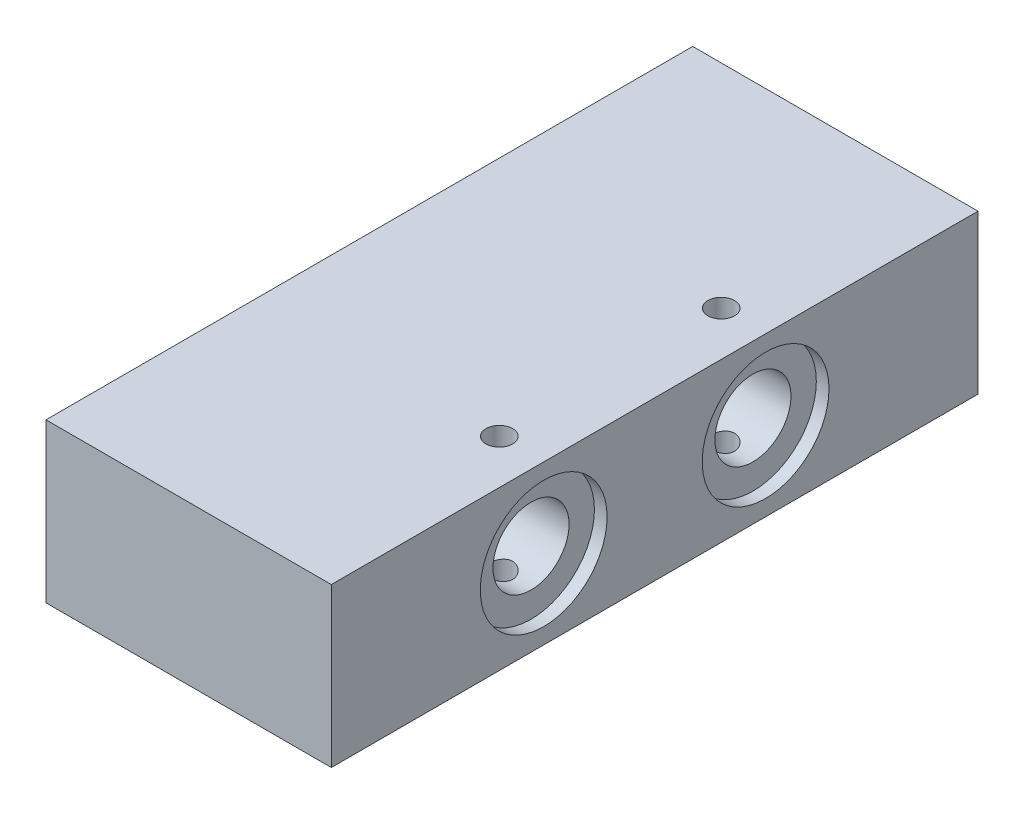
SolidWorks part; units mm, degrees
ref_plane "Front Plane" through (0, 0, 0) normal (0, 0, 1) x (1, 0, 0)
ref_plane "Top Plane" through (0, 0, 0) normal (0, 1, 0) x (1, 0, 0)
ref_plane "Right Plane" through (0, 0, 0) normal (1, 0, 0) x (0, 0, -1)
sketch "Sketch1" plane through (0, 0, 0) normal (0, 1, 0) x (1, 0, 0)
  line L1 (-22.5, -51) -> (22.5, -51)
  line L2 (-22.5, -51) -> (-22.5, 51)
  line L3 (-22.5, 51) -> (22.5, 51)
  line L4 (22.5, -51) -> (22.5, 51)
  line L5 (-22.5, -51) -> (22.5, 51) construction
  line L6 (-22.5, 51) -> (22.5, -51) construction
  point P0 (0, 0)
  dimension "D1" = 45
  dimension "D2" = 102
extrude "Boss-Extrude1" add sketch "Sketch1" along normal blind 25
hole_wizard "M5 Tapped Hole3" positions "Sketch12" profile "Sketch13" tap size "M5" standard "DIN" end condition through all
sketch "Sketch12" plane through (0, 25, 0) normal (0, 1, 0) x (1, 0, 0)
  line L0 (22.5, -51) -> (22.5, 51) construction
  line L1 (-22.5, -51) -> (22.5, -51) construction
  point P0 (15.5, 17.5)
  point P2 (15.5, -17.5)
  dimension "D1" = 7
  dimension "D2" = 7
  dimension "D3" = 33.5
  dimension "D4" = 35
sketch "Sketch13" plane through (15.5, 25, -17.5) normal (1, 0, 0) x (0, 0, 1)
  line L0 (0, 0) -> (0, 25)
  line L1 (0, 25) -> (2.1, 25)
  line L2 (2.1, 25) -> (2.1, 0)
  line L5 (2.1, 0) -> (0, 0)
  line L11 (0, -6.35) -> (0, 107.95) construction
  dimension "Thru Tap Drill Dia." = 4.2
  dimension "Thru Tap Drill Depth" = 25
cosmetic thread "Hole Thread9" parameters "D2"=5
cosmetic thread "Hole Thread10" parameters "D2"=5
sketch "Sketch27" plane through (-22.5, 0, 0) normal (-1, 0, 0) x (0, 0, 1)
  line L0 (51, 25) -> (51, 0) construction
  line L1 (-51, 25) -> (51, 25) construction
  circle A0 centre (-17.5, 12.5) radius 6
  circle A1 centre (17.5, 12.5) radius 6
  dimension "D1" = 12
  dimension "D2" = 12
  dimension "D5" = 12.5
  dimension "D3" = 33.5
  dimension "D4" = 35
  dimension "D6" = 12.5
extrude "Cut-Extrude1" cut sketch "Sketch27" against normal blind 74
sketch "Sketch28" plane through (-22.5, 0, 0) normal (-1, 0, 0) x (0, 0, 1)
  circle A0 centre (-17.5, 12.5) radius 10
  circle A1 centre (17.5, 12.5) radius 10
  dimension "D1" = 20
  dimension "D2" = 20
extrude "Cut-Extrude3" cut sketch "Sketch28" against normal blind 2
sketch "Sketch30" plane through (22.5, 0, 0) normal (1, 0, 0) x (0, 0, -1)
  circle A0 centre (-17.5, 12.5) radius 10
  circle A1 centre (17.5, 12.5) radius 10
  dimension "D1" = 20
  dimension "D2" = 20
extrude "Cut-Extrude4" cut sketch "Sketch30" against normal blind 2
hole_wizard "M5 Tapped Hole4" positions "Sketch31" profile "Sketch32" tap size "M5" standard "DIN"
sketch "Sketch31" plane through (0, 0, -51) normal (0, 0, -1) x (-1, 0, 0)
  line L0 (22.5, 25) -> (22.5, 0) construction
  line L1 (-22.5, 25) -> (-22.5, 0) construction
  line L3 (-22.5, 0) -> (22.5, 0) construction
  line L4 (-22.5, 25) -> (22.5, 25) construction
  point P0 (-18, 5)
  point P2 (18, 20)
  point P13 (-15.7032, 0)
  point P20 (-56.0486, 27.3495)
  dimension "D1" = 4.5
  dimension "D2" = 4.5
  dimension "D3" = 5
  dimension "D4" = 5
sketch "Sketch32" plane through (18, 5, -51) normal (1, 0, 0) x (0, 1, 0)
  line L0 (0, 0) -> (0, 15.2618)
  line L1 (0, 15.2618) -> (2.1, 14)
  line L2 (2.1, 14) -> (2.1, 0)
  line L5 (2.1, 0) -> (0, 0)
  line L10 (0, 15.2618) -> (-2.1, 14) construction
  line L11 (0, -6.35) -> (0, 107.95) construction
  dimension "Tap Drill Dia." = 4.2
  dimension "Tap Drill Depth" = 14
  dimension "Drill Angle" = 118
cosmetic thread "Hole Thread11" parameters "D1"=10, "D2"=5
cosmetic thread "Hole Thread12" parameters "D1"=10, "D2"=5
